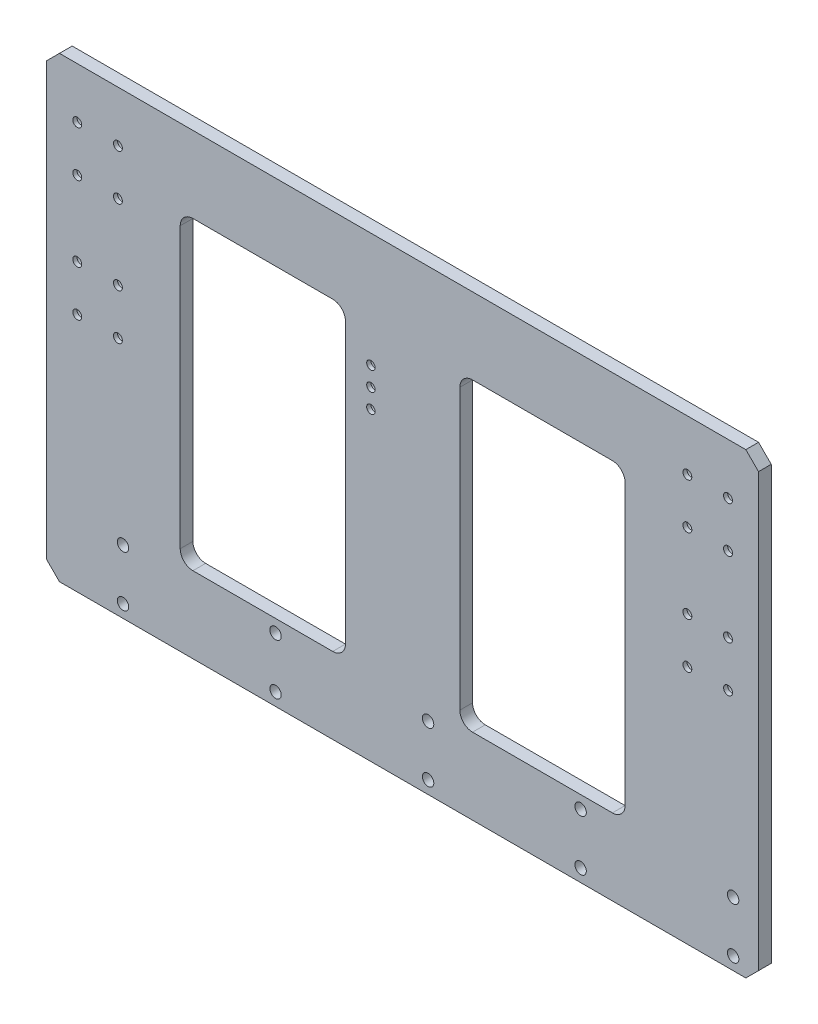
SolidWorks part; units mm, degrees
ref_plane "前视基准面" through (0, 0, 0) normal (0, 0, 1) x (1, 0, 0)
ref_plane "上视基准面" through (0, 0, 0) normal (0, 1, 0) x (1, 0, 0)
ref_plane "右视基准面" through (0, 0, 0) normal (1, 0, 0) x (0, 0, -1)
sketch "草图1" plane through (0, 0, 0) normal (0, 0, 1) x (1, 0, 0)
  line L0 (0, 210.9664) -> (0, -254.3523) construction
  line L1 (-270, 180) -> (270, 180)
  line L2 (-280, 170) -> (-280, -170)
  line L3 (-270, -180) -> (270, -180)
  line L4 (280, 170) -> (280, -170)
  line L5 (-280, 180) -> (280, -180) construction
  line L6 (-280, -180) -> (280, 180) construction
  line L7 (-165, 120) -> (-55, 120)
  line L8 (-175, 110) -> (-175, -110)
  line L9 (-165, -120) -> (-55, -120)
  line L10 (-45, 110) -> (-45, -110)
  line L11 (165, -120) -> (55, -120)
  line L12 (45, 110) -> (45, -110)
  line L13 (165, 120) -> (55, 120)
  line L14 (175, 110) -> (175, -110)
  line L15 (0, 0) -> (-477.2634, 0) construction
  line L16 (-256, 140) -> (-224, 140) construction
  line L17 (-256, 140) -> (-256, 104) construction
  line L18 (-256, 104) -> (-224, 104) construction
  line L19 (-224, 140) -> (-224, 104) construction
  line L20 (-280, 170) -> (-270, 180)
  line L21 (270, 180) -> (280, 170)
  line L22 (280, -170) -> (270, -180)
  line L23 (-280, -170) -> (-270, -180)
  arc A0 (-55, -120) -> (-45, -110) centre (-55, -110) ccw
  arc A1 (-165, -120) -> (-175, -110) centre (-165, -110) cw
  arc A2 (-45, 110) -> (-55, 120) centre (-55, 110) ccw
  arc A3 (-175, 110) -> (-165, 120) centre (-165, 110) cw
  arc A4 (55, -120) -> (45, -110) centre (55, -110) cw
  arc A5 (45, 110) -> (55, 120) centre (55, 110) cw
  arc A6 (165, -120) -> (175, -110) centre (165, -110) ccw
  arc A7 (175, 110) -> (165, 120) centre (165, 110) ccw
  circle A8 centre (-256, 140) radius 3.5
  circle A9 centre (-224, 140) radius 3.5
  circle A10 centre (-256, 104) radius 3.5
  circle A11 centre (-224, 104) radius 3.5
  circle A20 centre (256, 104) radius 3.5
  circle A21 centre (224, 104) radius 3.5
  circle A22 centre (224, 140) radius 3.5
  circle A23 centre (256, 140) radius 3.5
  circle A24 centre (-220, -130) radius 4.5
  circle A25 centre (-100, -130) radius 4.5
  circle A26 centre (20, -130) radius 4.5
  circle A27 centre (140, -130) radius 4.5
  circle A28 centre (260, -130) radius 4.5
  circle A29 centre (-100, -170) radius 4.5
  circle A30 centre (20, -170) radius 4.5
  circle A31 centre (140, -170) radius 4.5
  circle A32 centre (260, -170) radius 4.5
  circle A33 centre (-220, -170) radius 4.5
  circle A34 centre (-25, 90) radius 1.5
  circle A37 centre (-256, 45) radius 3.5
  circle A38 centre (-224, 45) radius 3.5
  circle A39 centre (-25, 75) radius 1.5
  circle A40 centre (-25, 60) radius 1.5
  circle A41 centre (-256, 9) radius 3.5
  circle A42 centre (-224, 9) radius 3.5
  circle A43 centre (224, 45) radius 3.5
  circle A44 centre (256, 45) radius 3.5
  circle A45 centre (224, 9) radius 3.5
  circle A46 centre (256, 9) radius 3.5
  point P0 (0, 0)
  point P20 (-45, 0)
  dimension "D3" = 10
  dimension "D9" = 60
  dimension "D10" = 50
  dimension "D11" = 9
  dimension "D12" = 5
  dimension "D17" = 3
  dimension "D1" = 560
  dimension "D2" = 360
  dimension "D4" = 240
  dimension "D5" = 130
  dimension "D6" = 0
  dimension "D7" = 45
  dimension "D8" = 32
  dimension "D13" = 36
  dimension "D14" = 40
  dimension "D15" = 24
  dimension "D23" = 20
  dimension "D24" = 90
  dimension "D22" = 2
  dimension "D16" = 2
  dimension "D25" = 3
extrude "凸台-拉伸1" add sketch "草图1" along normal blind 10
hole_wizard "打孔尺寸(%根据)内六角圆柱头螺钉的类型1" positions "3D草图1" profile "草图3" counterbore size "M6" standard "GB"
sketch3d "3D草图1"
  line L0 (224, 140, 10) -> (224, 140, 0) construction
  line L1 (256, 140, 10) -> (256, 140, 0) construction
  line L2 (256, 104, 10) -> (256, 104, 0) construction
  line L3 (224, 104, 10) -> (224, 104, 0) construction
  line L4 (256, 45, 10) -> (256, 45, 0) construction
  line L5 (224, 45, 10) -> (224, 45, 0) construction
  line L6 (256, 9, 10) -> (256, 9, 0) construction
  line L7 (224, 9, 10) -> (224, 9, 0) construction
  line L8 (-25, 90, 10) -> (-25, 90, 0) construction
  line L9 (-25, 75, 10) -> (-25, 75, 0) construction
  line L10 (-25, 60, 10) -> (-25, 60, 0) construction
  line L11 (-224, 140, 10) -> (-224, 140, 0) construction
  line L12 (-224, 104, 10) -> (-224, 104, 0) construction
  line L13 (-256, 104, 10) -> (-256, 104, 0) construction
  line L14 (-256, 140, 10) -> (-256, 140, 0) construction
  line L15 (-224, 45, 10) -> (-224, 45, 0) construction
  line L16 (-256, 45, 10) -> (-256, 45, 0) construction
  line L17 (-224, 9, 10) -> (-224, 9, 0) construction
  line L18 (-256, 9, 10) -> (-256, 9, 0) construction
  circle A0 centre (256, 140, 0) radius 3.5 construction
  circle A1 centre (224, 140, 10) radius 3.5 construction
  point P0 (256.4078, 136.5238, 0)
  point P4 (256, 140, 3.5)
  point P5 (224.4023, 136.5232, 10)
  point P9 (224, 140, 13.5)
  point P10 (224, 140, 0)
  point P14 (256, 140, 0)
  point P18 (256, 104, 0)
  point P22 (224, 104, 0)
  point P26 (256, 45, 0)
  point P30 (224, 45, 0)
  point P34 (256, 9, 0)
  point P38 (224, 9, 0)
  point P42 (-25, 90, 0)
  point P46 (-25, 75, 0)
  point P50 (-25, 60, 0)
  point P54 (-224, 140, 0)
  point P58 (-224, 104, 0)
  point P62 (-256, 104, 0)
  point P66 (-256, 140, 0)
  point P70 (-224, 45, 0)
  point P74 (-256, 45, 0)
  point P78 (-224, 9, 0)
  point P82 (-256, 9, 0)
sketch "草图3" plane through (-256, 9, 0) normal (1, 0, 0) x (0, 1, 0)
  line L0 (0, 0) -> (0, 19.9828)
  line L1 (0, 19.9828) -> (3.3, 18)
  line L2 (3.3, 18) -> (3.3, 6.8)
  line L3 (3.3, 6.8) -> (5.5, 6.8)
  line L4 (5.5, 6.8) -> (5.5, 0)
  line L5 (5.5, 0) -> (0, 0)
  line L10 (0, 19.9828) -> (-3.3, 18) construction
  line L11 (0, -6.35) -> (0, 107.95) construction
  dimension "孔直径" = 6.6
  dimension "孔深度" = 18
  dimension "柱形沉头孔直径" = 11
  dimension "柱形沉头孔深度" = 6.8
  dimension "导头角度" = 118
